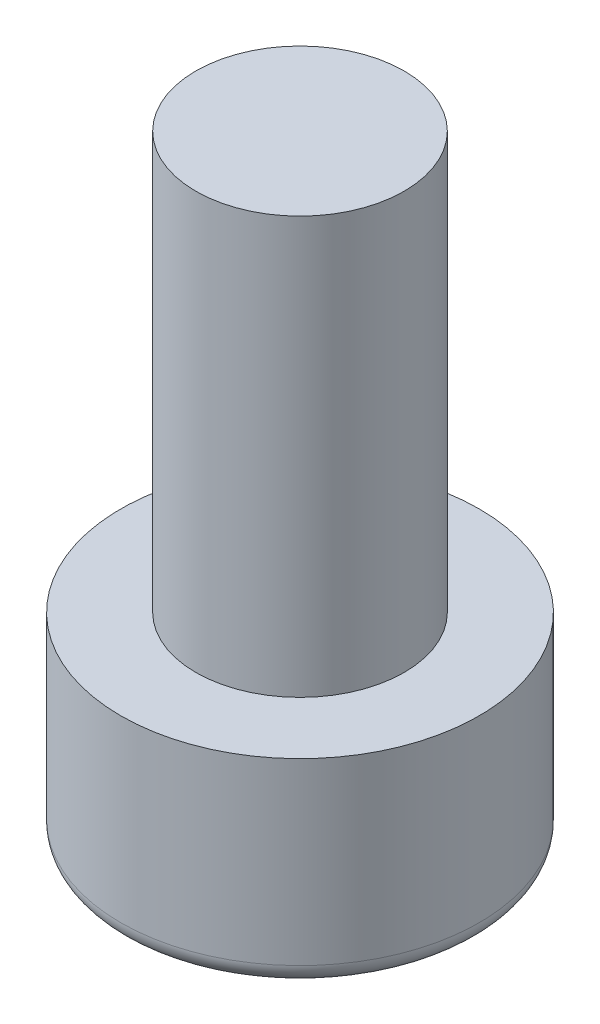
SolidWorks part; units mm, degrees
ref_plane "Front Plane" through (0, 0, 0) normal (0, 0, 1) x (1, 0, 0)
ref_plane "Top Plane" through (0, 0, 0) normal (0, 1, 0) x (1, 0, 0)
ref_plane "Right Plane" through (0, 0, 0) normal (1, 0, 0) x (0, 0, -1)
sketch "Sketch2" plane through (0, 0, 0) normal (0, 1, 0) x (1, 0, 0)
  circle A0 centre (0, 0) radius 4.3
  dimension "D1" = 8.6
extrude "Boss-Extrude1" add sketch "Sketch2" along normal blind 4.8
sketch "Sketch3" plane through (0, 4.8, 0) normal (0, 1, 0) x (1, 0, 0)
  circle A0 centre (0, 0) radius 2.5
  dimension "D1" = 5
extrude "Boss-Extrude2" add sketch "Sketch3" along normal blind 10
sketch "Sketch5" plane through (0, 0, 0) normal (0, -1, 0) x (1, 0, 0)
  line L1 (-1.1547, 2) -> (-2.3094, 0)
  line L2 (-2.3094, 0) -> (-1.1547, -2)
  line L3 (-1.1547, -2) -> (1.1547, -2)
  line L4 (1.1547, -2) -> (2.3094, 0)
  line L5 (2.3094, 0) -> (1.1547, 2)
  line L6 (1.1547, 2) -> (-1.1547, 2)
  circle A0 centre (0, 0) radius 2 construction
  dimension "D1" = 4
extrude "Cut-Extrude1" cut sketch "Sketch5" against normal blind 3.25
fillet "Fillet1" radius 0.5 13 edges at (-1.7321, 0, -1) (0, 0, -2) (1.7321, 0, -1) (1.7321, 0, 1) (0, 0, 2) (-1.7321, 0, 1) (0, 0, 4.3) (1.7321, 3.25, 1) (1.7321, 3.25, -1) (0, 3.25, -2) (-1.7321, 3.25, -1) (-1.7321, 3.25, 1) (0, 3.25, 2)
